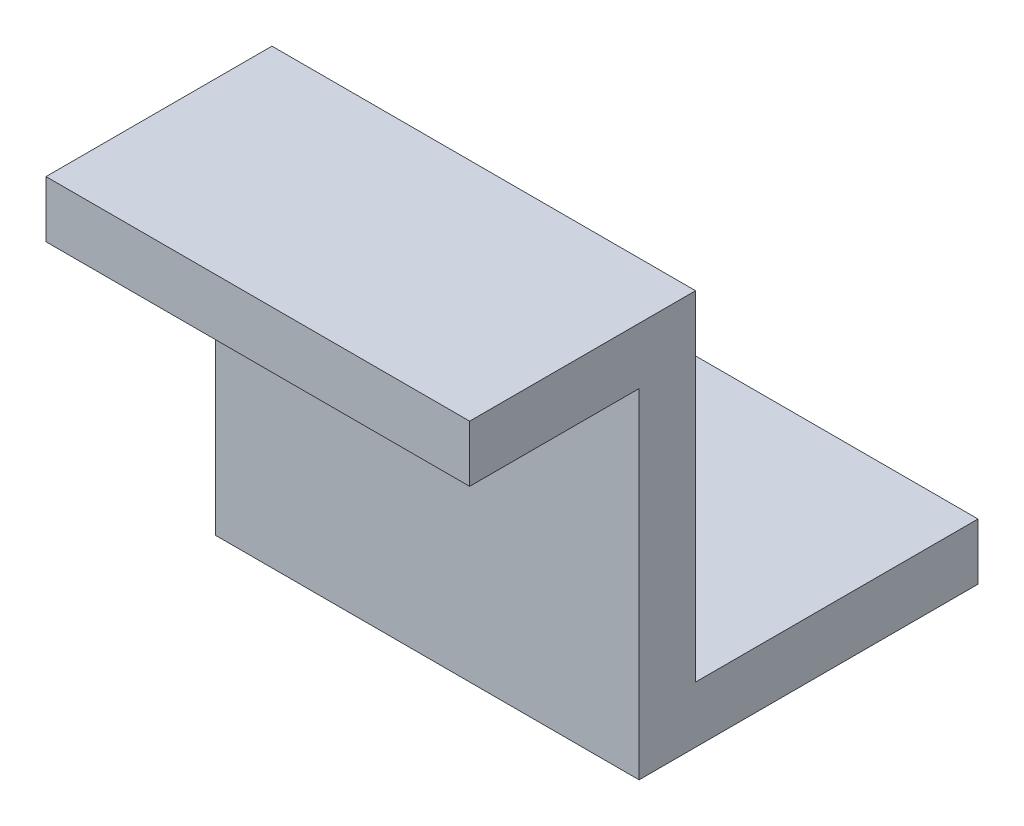
SolidWorks part; units mm, degrees
ref_plane "Front Plane" through (0, 0, 0) normal (0, 0, 1) x (1, 0, 0)
ref_plane "Top Plane" through (0, 0, 0) normal (0, 1, 0) x (1, 0, 0)
ref_plane "Right Plane" through (0, 0, 0) normal (1, 0, 0) x (0, 0, -1)
sketch "Sketch1" plane through (0, 0, 0) normal (1, 0, 0) x (0, 0, -1)
  line L0 (0, 0) -> (8, 0)
  line L1 (8, 0) -> (8, -12)
  line L2 (8, -12) -> (18, -12)
  line L3 (18, -12) -> (18, -14)
  line L4 (18, -14) -> (6, -14)
  line L5 (6, -14) -> (6, -2)
  line L6 (6, -2) -> (0, -2)
  line L7 (0, -2) -> (0, 0)
  dimension "D1" = 2
  dimension "D2" = 8
  dimension "D3" = 6
  dimension "D4" = 12
  dimension "D5" = 12
  dimension "D6" = 2
  dimension "D7" = 12
  dimension "D8" = 14
  dimension "D9" = 2
extrude "Boss-Extrude1" add sketch "Sketch1" against normal blind 15
sketch "Sketch3" plane through (0, -12, 0) normal (0, 1, 0) x (1, 0, 0)
  line L0 (-7.5, 18) -> (-7.5, 8) construction
  line L1 (-15, 18) -> (0, 18) construction
  line L2 (-15, 8) -> (0, 8) construction
  line L3 (0, 13) -> (-15, 13) construction
  line L4 (0, 18) -> (0, 8) construction
  line L5 (-15, 18) -> (-15, 8) construction
  circle A0 centre (-7.5, 13) radius 1.5
  dimension "D1" = 3
  dimension "D2" = 5
  dimension "D3" = 7.5
extrude "Cut-Extrude1" cut sketch "Sketch3" against normal up to next
